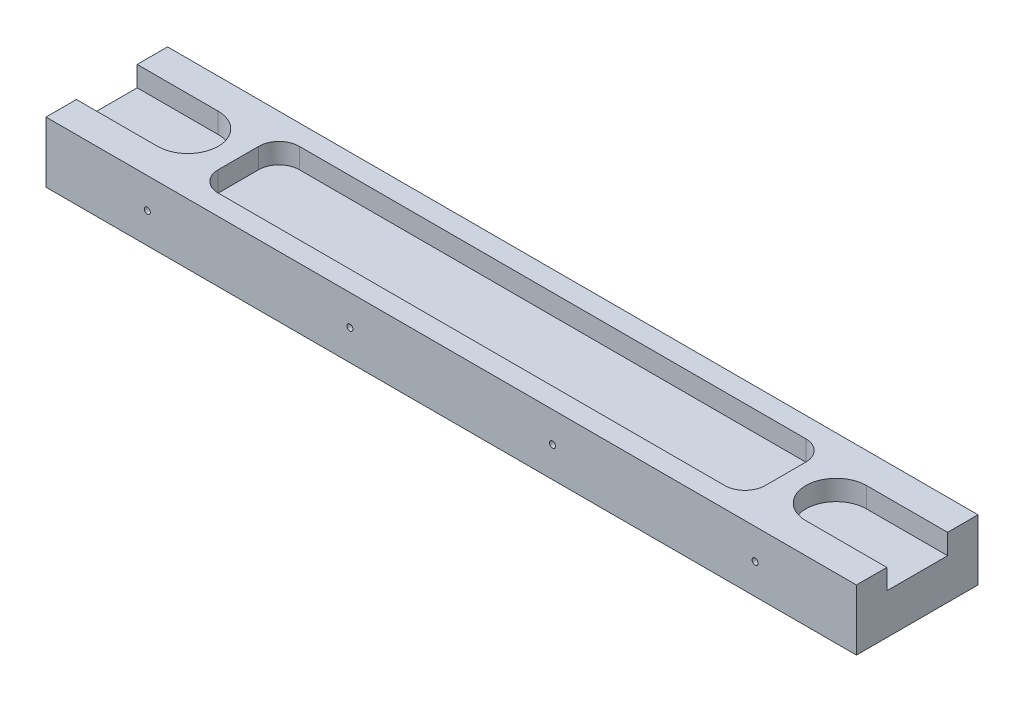
SolidWorks part; units mm, degrees
ref_plane "Front Plane" through (0, 0, 0) normal (0, 0, 1) x (1, 0, 0)
ref_plane "Top Plane" through (0, 0, 0) normal (0, 1, 0) x (1, 0, 0)
ref_plane "Right Plane" through (0, 0, 0) normal (1, 0, 0) x (0, 0, -1)
sketch "Sketch1" plane through (0, 0, 0) normal (0, 1, 0) x (1, 0, 0)
  line L1 (0, 0) -> (200, 0)
  line L2 (0, 0) -> (0, 30)
  line L3 (0, 30) -> (200, 30)
  line L4 (200, 0) -> (200, 30)
  dimension "D1" = 200
  dimension "D2" = 30
extrude "Boss-Extrude1" add sketch "Sketch1" along normal blind 15
sketch "Sketch2" plane through (0, 15, 0) normal (0, 1, 0) x (1, 0, 0)
  line L0 (-20, 15) -> (20, 15) construction
  line L1 (-20, 22.5) -> (20, 22.5)
  line L2 (-20, 7.5) -> (20, 7.5)
  line L3 (0, 30) -> (0, 0) construction
  line L4 (100, 30) -> (100, 0) construction
  line L5 (200, 30) -> (0, 30) construction
  line L6 (0, 0) -> (200, 0) construction
  line L7 (220, 15) -> (180, 15) construction
  line L8 (220, 22.5) -> (180, 22.5)
  line L9 (220, 7.5) -> (180, 7.5)
  arc A0 (-20, 22.5) -> (-20, 7.5) centre (-20, 15) ccw
  arc A1 (20, 7.5) -> (20, 22.5) centre (20, 15) ccw
  arc A2 (220, 22.5) -> (220, 7.5) centre (220, 15) cw
  arc A3 (180, 7.5) -> (180, 22.5) centre (180, 15) cw
  point P2 (0, 15)
  point P9 (0, 15)
  point P18 (200, 15)
  dimension "D1" = 40
  dimension "D2" = 15
extrude "Cut-Extrude1" cut sketch "Sketch2" against normal blind 5
sketch "Sketch3" plane through (0, 0, 0) normal (0, 0, 1) x (1, 0, 0)
  line L0 (0, 7.5) -> (200, 7.5) construction
  line L1 (0, 15) -> (0, 0) construction
  line L2 (200, 15) -> (200, 0) construction
  circle A0 centre (25, 7.5) radius 0.75
  circle A1 centre (75, 7.5) radius 0.75
  circle A2 centre (125, 7.5) radius 0.75
  circle A3 centre (175, 7.5) radius 0.75
  dimension "D1" = 1.5
  dimension "D2" = 25
  dimension "D3" = 4
extrude "Cut-Extrude2" cut sketch "Sketch3" against normal up to surface (30 mm away) up to face at (100, 7.5, -30)
sketch "Sketch4" plane through (0, 15, 0) normal (0, 1, 0) x (1, 0, 0)
  line L0 (200, 30) -> (0, 30) construction
  line L1 (37.5, 25) -> (162.5, 25)
  line L2 (32.5, 20) -> (32.5, 10)
  line L3 (37.5, 5) -> (162.5, 5)
  line L4 (167.5, 20) -> (167.5, 10)
  line L5 (0, 0) -> (200, 0) construction
  arc A0 (20, 7.5) -> (20, 22.5) centre (20, 15) ccw construction
  arc A1 (180, 22.5) -> (180, 7.5) centre (180, 15) ccw construction
  arc A2 (37.5, 25) -> (32.5, 20) centre (37.5, 20) ccw
  arc A3 (32.5, 10) -> (37.5, 5) centre (37.5, 10) ccw
  arc A4 (162.5, 5) -> (167.5, 10) centre (162.5, 10) ccw
  arc A5 (162.5, 25) -> (167.5, 20) centre (162.5, 20) cw
  point P4 (27.5, 15)
  point P5 (172.5, 15)
  dimension "D5" = 5
  dimension "D1" = 5
  dimension "D2" = 5
  dimension "D3" = 5
  dimension "D4" = 5
extrude "Cut-Extrude3" cut sketch "Sketch4" against normal blind 5
